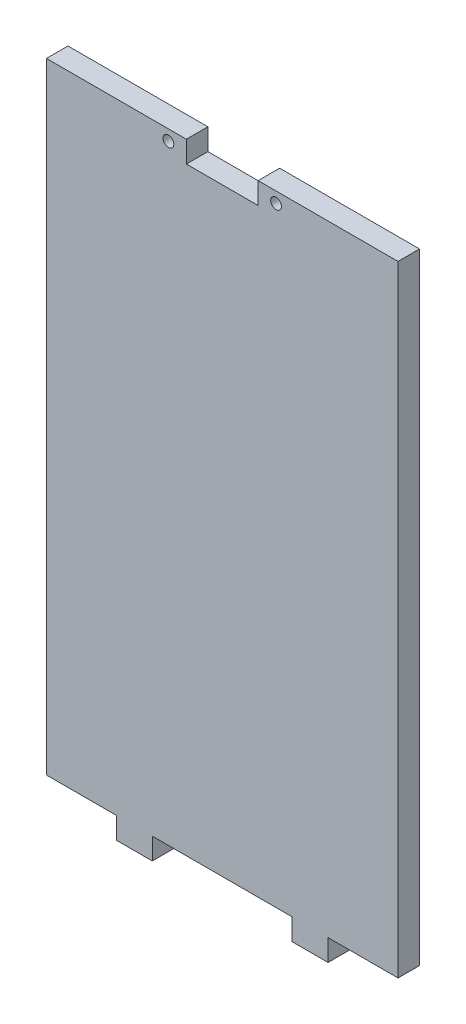
SolidWorks part; units mm, degrees
ref_plane "Plan de face" through (0, 0, 0) normal (0, 0, 1) x (1, 0, 0)
ref_plane "Plan de dessus" through (0, 0, 0) normal (0, 1, 0) x (1, 0, 0)
ref_plane "Plan de droite" through (0, 0, 0) normal (1, 0, 0) x (0, 0, -1)
sketch "Esquisse1" plane through (0, 0, 0) normal (0, 0, 1) x (1, 0, 0)
  line L0 (0, 176.8395) -> (0, -221.1538) construction
  line L1 (-49, 86.5) -> (49, 86.5)
  line L2 (-49, 86.5) -> (-49, -86.5)
  line L3 (-49, -86.5) -> (49, -86.5)
  line L4 (49, 86.5) -> (49, -86.5)
  line L5 (376.8436, 0) -> (-286.1998, 0) construction
  line L6 (-376.8436, 0) -> (286.1998, 0) construction
  dimension "D1" = 173
  dimension "D2" = 98
  dimension "D3" = 49
  dimension "D4" = 86.5
extrude "Boss.-Extru.1" add sketch "Esquisse1" along normal blind 6
sketch "Esquisse2" plane through (0, 0, 6) normal (0, 0, 1) x (1, 0, 0)
  line L1 (-49, -86.5) -> (49, -86.5) construction
  line L2 (29.5, -86.5) -> (19.5, -86.5)
  line L3 (29.5, -86.5) -> (29.5, -92.5)
  line L4 (29.5, -92.5) -> (19.5, -92.5)
  line L6 (154.6429, 0) -> (-167.6281, 0) construction
  line L7 (19.5, -86.5) -> (19.5, -92.5)
  line L8 (-49, 86.5) -> (-49, -86.5) construction
  line L9 (-19.5, -86.5) -> (-29.5, -86.5)
  line L10 (-19.5, -86.5) -> (-19.5, -92.5)
  line L11 (-19.5, -92.5) -> (-29.5, -92.5)
  line L12 (-29.5, -86.5) -> (-29.5, -92.5)
  dimension "D1" = 6
  dimension "D2" = 6
  dimension "D3" = 10
  dimension "D4" = 10
  dimension "D5" = 19.5
  dimension "D6" = 39
extrude "Boss.-Extru.2" add sketch "Esquisse2" against normal blind 6
sketch "Esquisse3" plane through (0, 0, 6) normal (0, 0, 1) x (1, 0, 0)
  line L0 (-49, 86.5) -> (-49, -86.5) construction
  line L2 (84.5882, 83.5) -> (-34.9143, 83.5) construction
  line L4 (49, -86.5) -> (49, 86.5) construction
  line L5 (49, 86.5) -> (-49, 86.5) construction
  circle A0 centre (-15, 83.5) radius 1.5
  circle A3 centre (15, 83.5) radius 1.5
  dimension "D1" = 3
  dimension "D2" = 3
  dimension "D3" = 34
  dimension "D4" = 34
  dimension "D5" = 3
extrude "Enlèv. mat.-Extru.1" cut sketch "Esquisse3" against normal blind 6
sketch "Esquisse4" plane through (0, 0, 6) normal (0, 0, 1) x (1, 0, 0)
  line L0 (49, 86.5) -> (-49, 86.5) construction
  line L1 (-10, 86.5) -> (10, 86.5)
  line L2 (-10, 86.5) -> (-10, 80.5)
  line L3 (-10, 80.5) -> (10, 80.5)
  line L4 (10, 86.5) -> (10, 80.5)
  line L5 (49, -86.5) -> (49, 86.5) construction
  dimension "D1" = 6
  dimension "D2" = 20
  dimension "D3" = 39
extrude "Enlèv. mat.-Extru.2" cut sketch "Esquisse4" against normal blind 6
equation "\"D3@Esquisse1\"=\"D2@Esquisse1\"/2"
equation "\"D4@Esquisse1\"=\"D1@Esquisse1\"/2"
